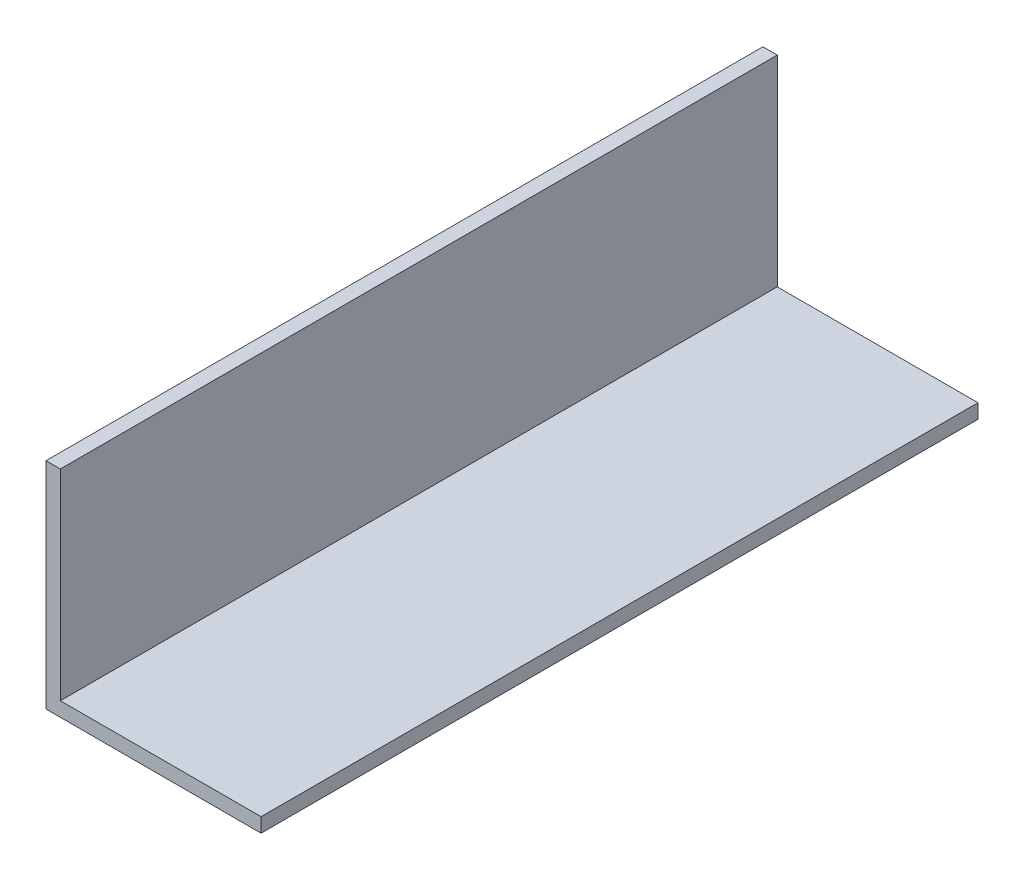
SolidWorks part; units mm, degrees
material "1060 合金"
ref_plane "正面" through (0, 0, 0) normal (0, 0, 1) x (1, 0, 0)
ref_plane "平面" through (0, 0, 0) normal (0, 1, 0) x (1, 0, 0)
ref_plane "右側面" through (0, 0, 0) normal (1, 0, 0) x (0, 0, -1)
sketch "ｽｹｯﾁ1" plane through (0, 0, 0) normal (0, 0, 1) x (1, 0, 0)
  line L1 (-5.4615, 6.3533) -> (9.5385, 6.3533)
  line L2 (-5.4615, 6.3533) -> (-5.4615, -8.6467)
  line L3 (-5.4615, -8.6467) -> (9.5385, -8.6467)
  line L4 (9.5385, 6.3533) -> (9.5385, -8.6467)
  line L5 (9.5385, 6.3533) -> (-4.4615, 6.3533)
  line L6 (9.5385, 6.3533) -> (9.5385, -7.6467)
  line L7 (9.5385, -7.6467) -> (-4.4615, -7.6467)
  line L8 (-4.4615, 6.3533) -> (-4.4615, -7.6467)
  dimension "D1" = 15
  dimension "D2" = 15
  dimension "D3" = 1
  dimension "D4" = 1
extrude "ﾎﾞｽ - 押し出し1" add sketch "ｽｹｯﾁ1" along normal blind 50 contours L8 L1 L2 L3 L4 L7
